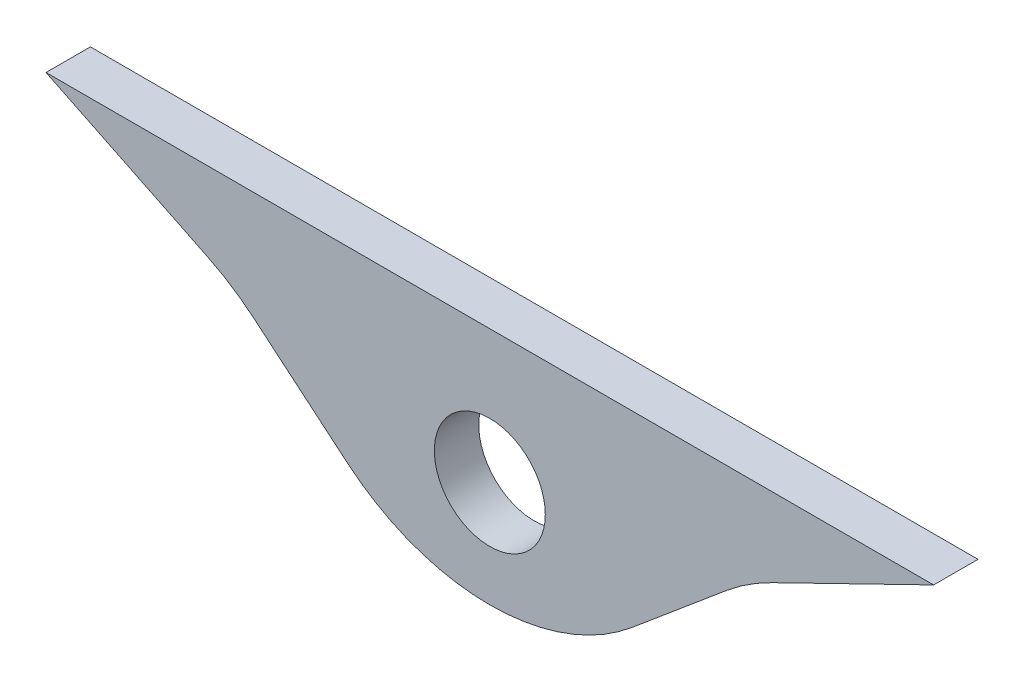
SolidWorks part; units mm, degrees
material "ﾊﾞﾙｻ"
ref_plane "正面" through (0, 0, 0) normal (0, 0, 1) x (1, 0, 0)
ref_plane "平面" through (0, 0, 0) normal (0, 1, 0) x (1, 0, 0)
ref_plane "右側面" through (0, 0, 0) normal (1, 0, 0) x (0, 0, -1)
sketch "ｽｹｯﾁ1" plane through (0, 0, 0) normal (0, 0, 1) x (1, 0, 0)
  line L0 (0, 0) -> (0, 38.4947) construction
  line L1 (0, -7.8324) -> (11.6055, 1.9057)
  line L2 (11.6055, 1.9057) -> (20, 6)
  line L3 (-11.6055, 1.9057) -> (-20, 6)
  line L4 (0, -7.8324) -> (-11.6055, 1.9057)
  line L5 (20, 6) -> (-20, 6)
  circle A0 centre (0, 0) radius 2.5
  point P8 (0, 6)
  dimension "D3" = 5
  dimension "D1" = 50
  dimension "D2" = 6
  dimension "D4" = 6
  dimension "D5" = 20
  dimension "D6" = 26
extrude "ﾎﾞｽ - 押し出し1" add sketch "ｽｹｯﾁ1" along normal blind 2
fillet "ﾌｨﾚｯﾄ1" radius 10 3 edges at (-11.6055, 1.9057, 1) (11.6055, 1.9057, 1) (0, -7.8324, 1)
